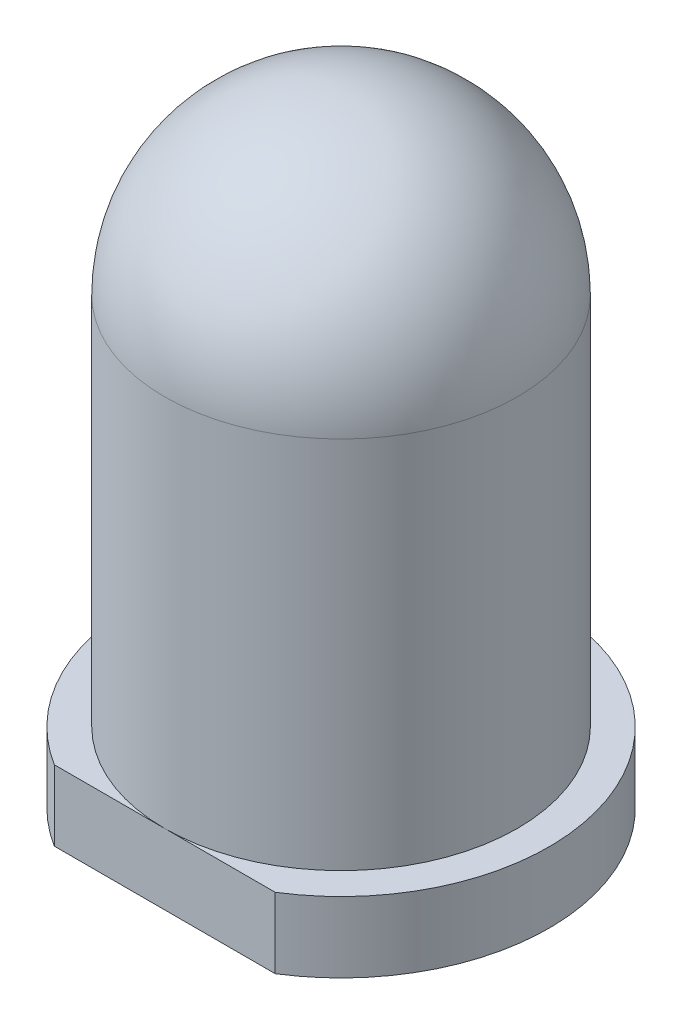
SolidWorks part; units mm, degrees
ref_plane "Front Plane" through (0, 0, 0) normal (0, 0, 1) x (1, 0, 0)
ref_plane "Top Plane" through (0, 0, 0) normal (0, 1, 0) x (1, 0, 0)
ref_plane "Right Plane" through (0, 0, 0) normal (1, 0, 0) x (0, 0, -1)
sketch "Sketch1" plane through (0, 0, 0) normal (0, 1, 0) x (1, 0, 0)
  circle A2 centre (0, 0) radius 2.95
  dimension "D1" = 5.9
extrude "Boss-Extrude4" add sketch "Sketch1" along normal blind 1 contours A2
sketch "Sketch2" plane through (0, 1, 0) normal (0, 1, 0) x (1, 0, 0)
  line L0 (0, -6.3697) -> (0, 7.1441) construction
  circle A0 centre (0, 0) radius 2.5
  dimension "D1" = 5
extrude "Boss-Extrude5" add sketch "Sketch2" along normal blind 7.8
ref_plane "Plane1" through (0, 0, 0) normal (1, 0, 0) x (0, 0, -1)
sketch "Sketch3" plane through (0, 0, 0) normal (1, 0, 0) x (0, 0, -1)
  line L0 (2.5, 8.8) -> (-2.5, 8.8) construction
  line L1 (0, 8.8) -> (-2.5, 8.8) construction
  line L2 (0, 11.1331) -> (0, -0.5069) construction
  line L3 (-2.5, 15.5376) -> (-2.5, 2.0624) construction
  line L7 (-2.5, 6.3) -> (-2.5, 1)
  line L8 (2.5, 1) -> (-2.5, 1) construction
  line L9 (-2.5, 1) -> (0, 1)
  line L13 (-2.5, 1) -> (-5.4499, 1)
  line L14 (-6.3697, 1) -> (7.1441, 1) construction
  line L15 (-5.4499, 1) -> (-5.4499, 10.7278)
  line L16 (-5.4499, 10.7278) -> (0, 10.7278)
  line L19 (0, 8.8) -> (0, 10.7278)
  arc A2 (0, 8.8) -> (-2.5, 6.3) centre (0, 6.3) ccw
revolve "Cut-Revolve5" cut sketch "Sketch3" angle 360 about L2
sketch "Sketch4" plane through (0, 1, 0) normal (0, 1, 0) x (1, 0, 0)
  line L0 (-6.7297, -2.5) -> (9.8573, -2.5)
  line L1 (-6.7297, -2.5) -> (-6.7297, -6.2882)
  line L2 (-6.7297, -6.2882) -> (9.8573, -6.2882)
  line L3 (9.8573, -6.2882) -> (9.8573, -2.5)
extrude "Cut-Extrude2" cut sketch "Sketch4" against normal through all both and the other way through all
